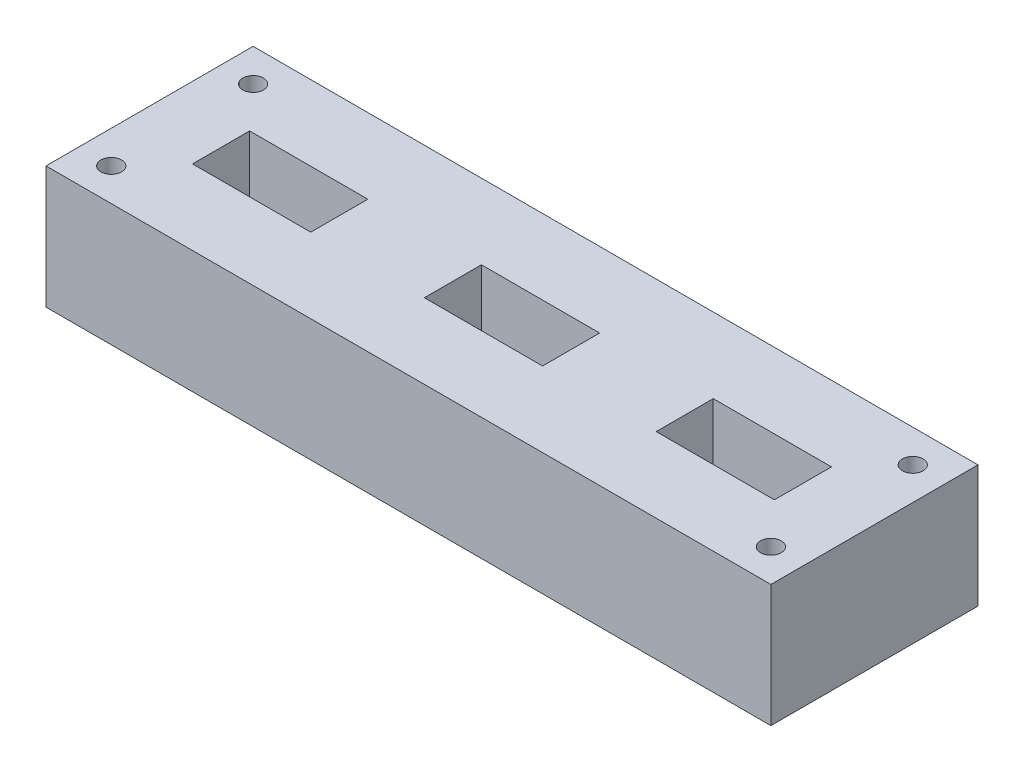
SolidWorks part; units mm, degrees
ref_plane "Front Plane" through (0, 0, 0) normal (0, 0, 1) x (1, 0, 0)
ref_plane "Top Plane" through (0, 0, 0) normal (0, 1, 0) x (1, 0, 0)
ref_plane "Right Plane" through (0, 0, 0) normal (1, 0, 0) x (0, 0, -1)
sketch "Sketch1" plane through (0, 0, 0) normal (0, 1, 0) x (1, 0, 0)
  line L0 (-55, 0) -> (55, 0) construction
  line L1 (-44.45, 12.7) -> (44.45, 12.7)
  line L2 (-44.45, 12.7) -> (-44.45, -12.7)
  line L3 (-44.45, -12.7) -> (44.45, -12.7)
  line L4 (44.45, 12.7) -> (44.45, -12.7)
  line L5 (0, -55) -> (0, 55) construction
  dimension "D1" = 88.9
  dimension "D2" = 25.4
  dimension "D3" = 12.7
  dimension "D4" = 44.45
extrude "Boss-Extrude1" add sketch "Sketch1" along normal blind 15
sketch "Sketch2" plane through (0, 15, 0) normal (0, 1, 0) x (1, 0, 0)
  line L0 (-8.25, 0) -> (8.25, 0) construction
  line L1 (-7.25, 3.5) -> (7.25, 3.5)
  line L2 (-7.25, 3.5) -> (-7.25, -3.5)
  line L3 (-7.25, -3.5) -> (7.25, -3.5)
  line L4 (7.25, 3.5) -> (7.25, -3.5)
  line L5 (0, -8.25) -> (0, 8.25) construction
  line L6 (-35.68, 3.5) -> (-21.18, 3.5)
  line L7 (-35.68, 3.5) -> (-35.68, -3.5)
  line L8 (-35.68, -3.5) -> (-21.18, -3.5)
  line L9 (-21.18, 3.5) -> (-21.18, -3.5)
  line L10 (21.18, 3.5) -> (35.68, 3.5)
  line L11 (21.18, 3.5) -> (21.18, -3.5)
  line L12 (21.18, -3.5) -> (35.68, -3.5)
  line L13 (35.68, 3.5) -> (35.68, -3.5)
  dimension "D1" = 14.5
  dimension "D2" = 7
  dimension "D3" = 3.5
  dimension "D4" = 7.25
  dimension "D5" = 14.5
  dimension "D6" = 7
  dimension "D7" = 3.5
  dimension "D8" = 13.93
  dimension "D9" = 14.5
  dimension "D10" = 7
  dimension "D11" = 3.5
  dimension "D12" = 13.93
extrude "Cut-Extrude1" cut sketch "Sketch2" against normal blind 25.4
sketch "Sketch3" plane through (0, 15, 0) normal (0, 1, 0) x (1, 0, 0)
  line L0 (44.45, 12.7) -> (-44.45, 12.7) construction
  line L1 (-44.45, 12.7) -> (-44.45, -12.7) construction
  line L2 (44.45, -12.7) -> (44.45, 12.7) construction
  line L3 (-44.45, -12.7) -> (44.45, -12.7) construction
  circle A0 centre (-40.45, 8.7) radius 1.27
  circle A1 centre (40.45, 8.7) radius 1.27
  circle A2 centre (-40.45, -8.7) radius 1.27
  circle A3 centre (40.45, -8.7) radius 1.27
  dimension "D1" = 2.54
  dimension "D4" = 2.54
  dimension "D7" = 2.54
  dimension "D10" = 2.54
  dimension "D2" = 4
  dimension "D3" = 4
  dimension "D5" = 4
  dimension "D6" = 4
  dimension "D8" = 4
  dimension "D9" = 4
  dimension "D11" = 4
  dimension "D12" = 4
extrude "Cut-Extrude3" cut sketch "Sketch3" against normal blind 25.4
